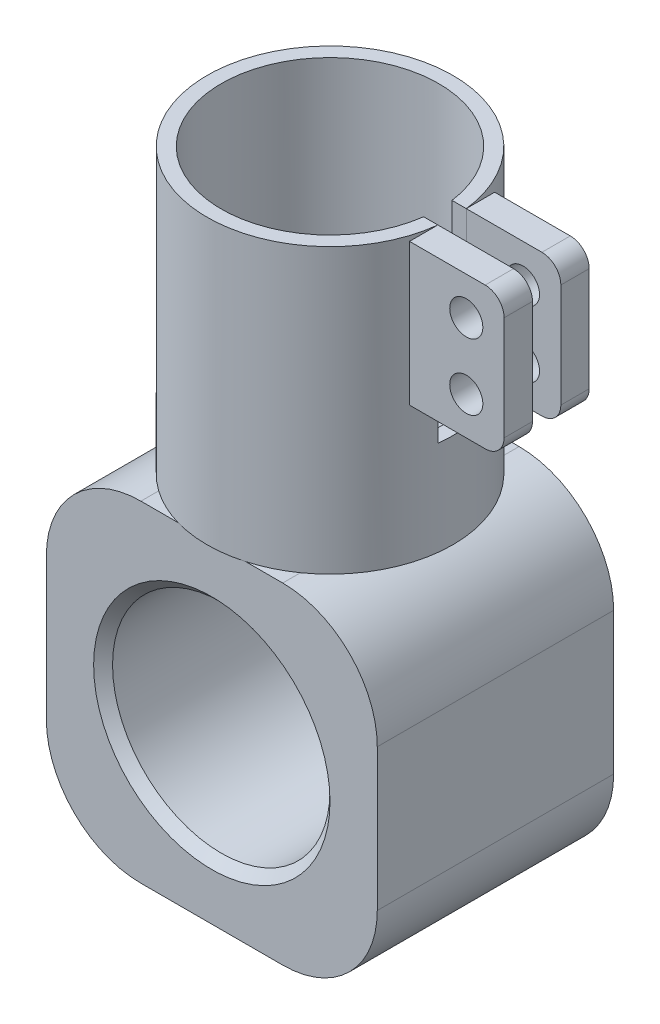
SolidWorks part; units mm, degrees
ref_plane "Front Plane" through (0, 0, 0) normal (0, 0, 1) x (1, 0, 0)
ref_plane "Top Plane" through (0, 0, 0) normal (0, 1, 0) x (1, 0, 0)
ref_plane "Right Plane" through (0, 0, 0) normal (1, 0, 0) x (0, 0, -1)
sketch "Sketch1" plane through (0, 0, 0) normal (0, 0, 1) x (1, 0, 0)
  line L1 (-7.5, 17.5) -> (7.5, 17.5)
  line L2 (-17.5, 7.5) -> (-17.5, -7.5)
  line L3 (-7.5, -17.5) -> (7.5, -17.5)
  line L4 (17.5, 7.5) -> (17.5, -7.5)
  line L5 (-17.5, 17.5) -> (17.5, -17.5) construction
  line L6 (-17.5, -17.5) -> (17.5, 17.5) construction
  circle A0 centre (0, 0) radius 11.5
  arc A1 (-17.5, -7.5) -> (-7.5, -17.5) centre (-7.5, -7.5) ccw
  arc A2 (7.5, -17.5) -> (17.5, -7.5) centre (7.5, -7.5) ccw
  arc A3 (7.5, 17.5) -> (17.5, 7.5) centre (7.5, 7.5) cw
  arc A4 (-7.5, 17.5) -> (-17.5, 7.5) centre (-7.5, 7.5) ccw
  point P0 (0, 0)
  dimension "D3" = 23
  dimension "D4" = 10
  dimension "D1" = 35
  dimension "D2" = 35
extrude "Boss-Extrude2" add sketch "Sketch1" along normal mid plane 25
sketch "Sketch4" plane through (0, 17.5, 0) normal (0, 1, 0) x (1, 0, 0)
  circle A0 centre (0, 0) radius 13
  circle A1 centre (0, 0) radius 11.5
  dimension "D1" = 26
  dimension "D2" = 23
extrude "Boss-Extrude3" add sketch "Sketch4" along normal blind 30
sketch "Sketch5" plane through (0, 0, 0) normal (0, 0, 1) x (1, 0, 0)
  line L0 (11.5, 47.5) -> (-11.5, 47.5) construction
  line L1 (5.9569, 47.5) -> (17.7624, 47.5)
  line L2 (5.9569, 47.5) -> (5.9569, 27.5)
  line L3 (5.9569, 27.5) -> (17.7624, 27.5)
  line L4 (17.7624, 47.5) -> (17.7624, 27.5)
  dimension "D1" = 20
extrude "Cut-Extrude1" cut sketch "Sketch5" against normal mid plane 3
sketch "Sketch7" plane through (0, 0, 1.5) normal (0, 0, -1) x (-1, 0, 0)
  line L1 (-12.9132, 47.5) -> (-20.9132, 47.5)
  line L2 (-12.9132, 47.5) -> (-12.9132, 32.5)
  line L3 (-12.9132, 32.5) -> (-20.9132, 32.5)
  line L4 (-22.9132, 45.5) -> (-22.9132, 34.5)
  arc A0 (-20.9132, 32.5) -> (-22.9132, 34.5) centre (-20.9132, 34.5) cw
  arc A1 (-20.9132, 47.5) -> (-22.9132, 45.5) centre (-20.9132, 45.5) ccw
  circle A2 centre (-18.9132, 43.5) radius 1.75
  circle A3 centre (-18.9132, 36.5) radius 1.75
  point P7 (-22.9132, 32.5)
  point P10 (-22.9132, 47.5)
  dimension "D3" = 2
  dimension "D4" = 4
  dimension "D7" = 3.5
  dimension "D1" = 15
  dimension "D2" = 10
  dimension "D5" = 7
  dimension "D6" = 6
extrude "Boss-Extrude4" add sketch "Sketch7" against normal blind 3 separate body
sketch "Sketch8" plane through (0, 0, -1.5) normal (0, 0, 1) x (1, 0, 0)
  line L4 (12.9132, 47.5) -> (12.9132, 32.5)
  line L5 (12.9132, 32.5) -> (20.9132, 32.5)
  line L6 (22.9132, 34.5) -> (22.9132, 45.5)
  line L7 (20.9132, 47.5) -> (12.9132, 47.5)
  line L8 (12.9132, 47.5) -> (12.9132, 32.5)
  line L9 (12.9132, 32.5) -> (20.9132, 32.5)
  line L10 (22.9132, 34.5) -> (22.9132, 45.5)
  line L11 (20.9132, 47.5) -> (12.9132, 47.5)
  circle A0 centre (18.9132, 36.5) radius 1.75 construction
  circle A1 centre (18.9132, 43.5) radius 1.75 construction
  circle A2 centre (18.9132, 36.5) radius 1.75
  circle A3 centre (18.9132, 43.5) radius 1.75
  arc A6 (20.9132, 32.5) -> (22.9132, 34.5) centre (20.9132, 34.5) ccw
  arc A7 (22.9132, 45.5) -> (20.9132, 47.5) centre (20.9132, 45.5) ccw
  arc A8 (20.9132, 32.5) -> (22.9132, 34.5) centre (20.9132, 34.5) ccw
  arc A9 (22.9132, 45.5) -> (20.9132, 47.5) centre (20.9132, 45.5) ccw
  dimension "D1" = 0
extrude "Boss-Extrude6" add sketch "Sketch8" against normal blind 3 separate body
chamfer "Chamfer1" distance 1 angle 45 2 edges at (11.5, 0, -12.5) (11.5, 0, 12.5)
